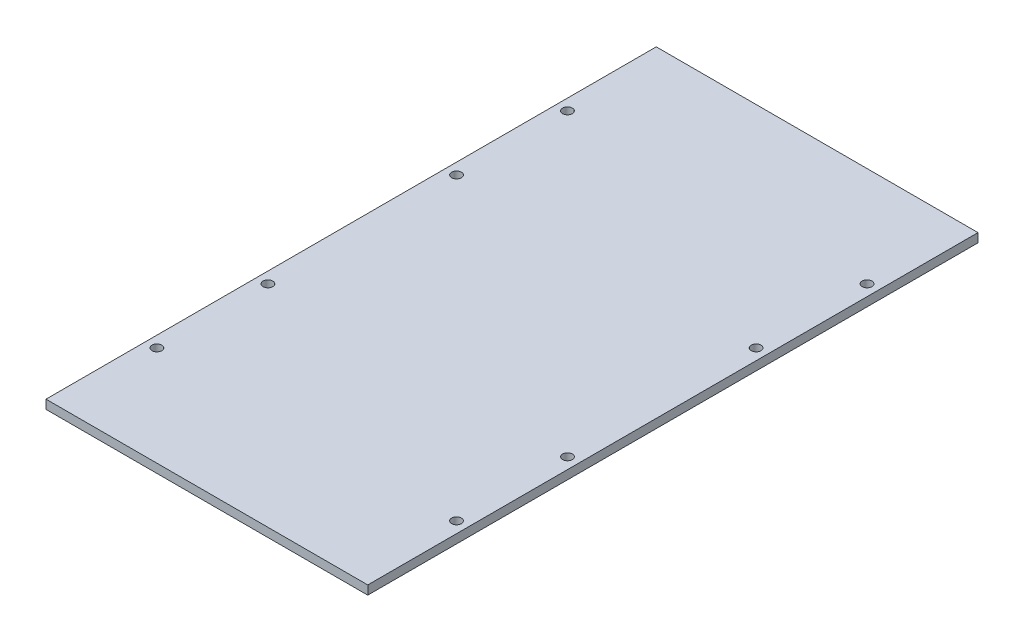
SolidWorks part; units mm, degrees
ref_plane "Front Plane" through (0, 0, 0) normal (0, 0, 1) x (1, 0, 0)
ref_plane "Top Plane" through (0, 0, 0) normal (0, 1, 0) x (1, 0, 0)
ref_plane "Right Plane" through (0, 0, 0) normal (1, 0, 0) x (0, 0, -1)
sketch "Sketch2" plane through (0, 0, 0) normal (0, 1, 0) x (1, 0, 0)
  line L1 (72.5, -137.5) -> (-72.5, -137.5)
  line L2 (72.5, -137.5) -> (72.5, 137.5)
  line L3 (72.5, 137.5) -> (-72.5, 137.5)
  line L4 (-72.5, -137.5) -> (-72.5, 137.5)
  line L5 (72.5, -137.5) -> (-72.5, 137.5) construction
  line L6 (72.5, 137.5) -> (-72.5, -137.5) construction
  point P0 (0, 0)
  dimension "D1" = 275
  dimension "D2" = 145
extrude "Boss-Extrude1" add sketch "Sketch2" along normal blind 4
sketch "Sketch3" plane through (0, 4, 0) normal (0, 1, 0) x (1, 0, 0)
  line L0 (72.5, 137.5) -> (-72.5, 137.5) construction
  line L1 (-72.5, 137.5) -> (-72.5, -137.5) construction
  line L2 (0, 168.3143) -> (0, -167.8661) construction
  line L3 (-125.5239, 0) -> (126.9359, 0) construction
  circle A0 centre (-67.5, 92.5) radius 2.2
  circle A1 centre (-67.5, 42.5) radius 2.2
  circle A2 centre (-67.5, -42.5) radius 2.2
  circle A3 centre (-67.5, -92.5) radius 2.2
  circle A4 centre (67.5, -92.5) radius 2.2
  circle A5 centre (67.5, -42.5) radius 2.2
  circle A6 centre (67.5, 42.5) radius 2.2
  circle A7 centre (67.5, 92.5) radius 2.2
  dimension "D1" = 4.4
  dimension "D4" = 95
  dimension "D2" = 45
  dimension "D3" = 5
  dimension "D5" = 85
  dimension "D6" = 50
extrude "Cut-Extrude1" cut sketch "Sketch3" against normal through all
